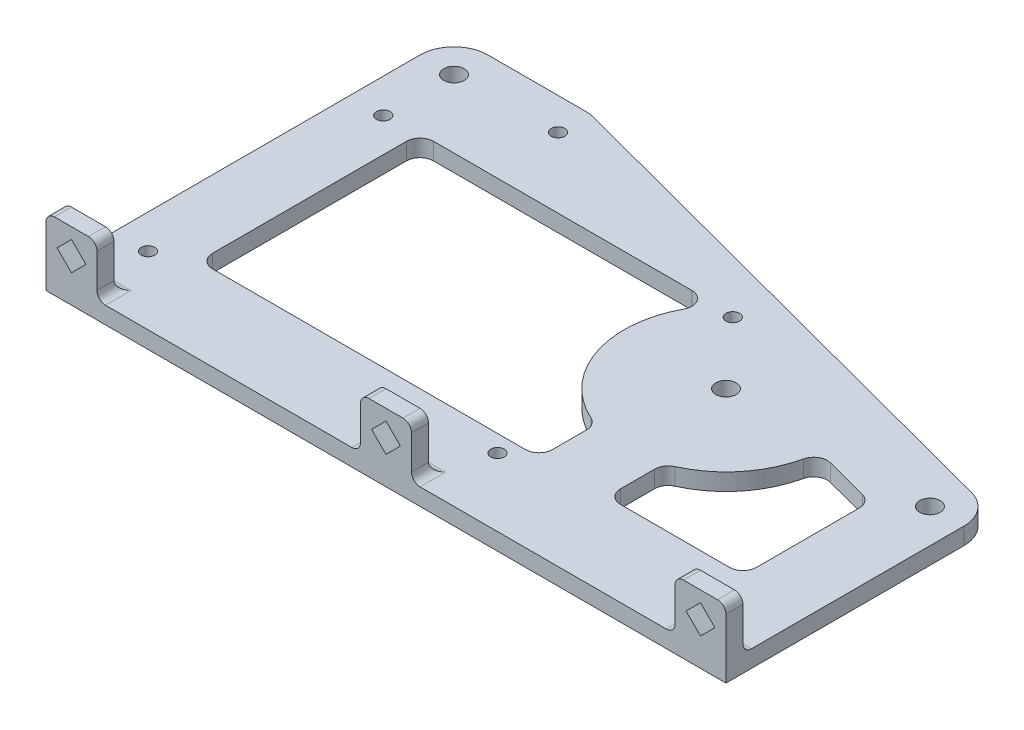
SolidWorks part; units mm, degrees
ref_plane "Front Plane" through (0, 0, 0) normal (0, 0, 1) x (1, 0, 0)
ref_plane "Top Plane" through (0, 0, 0) normal (0, 1, 0) x (1, 0, 0)
ref_plane "Right Plane" through (0, 0, 0) normal (1, 0, 0) x (0, 0, -1)
sketch "Sketch1" plane through (0, 0, 0) normal (0, 1, 0) x (1, 0, 0)
  line L0 (-57.15, 25.7742) -> (169.7943, 86.5838) construction
  line L1 (-48.962, 19.7507) -> (-53.0707, 35.0848) construction
  line L2 (-48.962, 19.7507) -> (171.8486, 78.9167) construction
  line L3 (-53.0707, 35.0848) -> (167.7399, 94.2508) construction
  line L4 (171.8486, 78.9167) -> (167.7399, 94.2508) construction
  line L5 (0, 0) -> (38.1, 0) construction
  line L6 (-82.55, 31.75) -> (-82.55, -44.45)
  line L7 (-82.55, -44.45) -> (44.45, -44.45)
  line L8 (44.45, -44.45) -> (44.45, 4.8894)
  line L9 (44.45, 4.8894) -> (-57.15, 31.75)
  line L10 (-57.15, 31.75) -> (-82.55, 31.75)
  circle A0 centre (0, 0) radius 1.905
  circle A1 centre (0, 12.7) radius 1.27 construction
  circle A2 centre (12.7, 0) radius 1.27 construction
  circle A3 centre (0, -12.7) radius 1.27 construction
  circle A4 centre (-12.7, 0) radius 1.27 construction
  circle A5 centre (0, 0) radius 12.7 construction
  circle A6 centre (-57.15, 25.7742) radius 1.27
  circle A7 centre (0, 0) radius 31.75 construction
  circle A8 centre (-76.2, 25.4) radius 1.905
  circle A9 centre (38.1, 0) radius 1.905
  dimension "D1" = 3.81
  dimension "D2" = 2.54
  dimension "D3" = 25.4
  dimension "D5" = 63.5
  dimension "D10" = 2.54
  dimension "D11" = 3.81
  dimension "D14" = 3.81
  dimension "D4" = 57.15
  dimension "D6" = 15.875
  dimension "D7" = 15
  dimension "D8" = 228.6
  dimension "D9" = 6.35
  dimension "D12" = 25.4
  dimension "D13" = 76.2
  dimension "D15" = 38.1
  dimension "D16" = 6.35
  dimension "D17" = 6.35
  dimension "D18" = 6.35
  dimension "D19" = 6.35
  dimension "D20" = 25.4
  dimension "D21" = 76.2
extrude "Boss-Extrude1" add sketch "Sketch1" along normal blind 3.175
sketch "Sketch2" plane through (0, 3.175, 0) normal (0, 1, 0) x (1, 0, 0)
  line L0 (-69.85, 10.16) -> (-69.85, -26.035)
  line L1 (-67.31, -28.575) -> (-8.89, -28.575)
  line L2 (-6.35, -26.035) -> (-6.35, -19.6748)
  line L3 (-82.55, 31.75) -> (-82.55, -44.45) construction
  line L4 (-19.05, 12.7) -> (-67.31, 12.7)
  line L5 (-57.15, 31.75) -> (-82.55, 31.75) construction
  line L6 (-82.55, -44.45) -> (44.45, -44.45) construction
  line L7 (6.35, -19.6748) -> (6.35, -26.035)
  line L8 (8.89, -28.575) -> (29.21, -28.575)
  line L9 (31.75, -26.035) -> (31.75, -6.8451)
  line L10 (29.8592, -4.3895) -> (21.7227, -2.2384)
  line L11 (44.45, -44.45) -> (44.45, 4.8894) construction
  line L12 (44.45, 4.8894) -> (-57.15, 31.75) construction
  arc A0 (-7.8441, -17.3601) -> (-16.8088, 8.9647) centre (0, 0) cw
  arc A1 (7.8441, -17.3601) -> (18.5943, -4.1418) centre (0, 0) ccw
  arc A2 (29.8592, -4.3895) -> (31.75, -6.8451) centre (29.21, -6.8451) cw
  arc A3 (29.21, -28.575) -> (31.75, -26.035) centre (29.21, -26.035) ccw
  arc A4 (8.89, -28.575) -> (6.35, -26.035) centre (8.89, -26.035) cw
  arc A5 (6.35, -19.6748) -> (7.8441, -17.3601) centre (8.89, -19.6748) cw
  arc A6 (18.5943, -4.1418) -> (21.7227, -2.2384) centre (21.0735, -4.694) cw
  arc A7 (-19.05, 12.7) -> (-16.8088, 8.9647) centre (-19.05, 10.16) cw
  arc A8 (-6.35, -19.6748) -> (-7.8441, -17.3601) centre (-8.89, -19.6748) ccw
  arc A9 (-8.89, -28.575) -> (-6.35, -26.035) centre (-8.89, -26.035) ccw
  arc A10 (-67.31, -28.575) -> (-69.85, -26.035) centre (-67.31, -26.035) cw
  arc A11 (-69.85, 10.16) -> (-67.31, 12.7) centre (-67.31, 10.16) cw
  circle A12 centre (-76.2, 12.192) radius 1.27
  circle A13 centre (-10.922, 12.192) radius 1.27
  circle A14 centre (-10.922, -31.75) radius 1.27
  circle A15 centre (-76.2, -31.75) radius 1.27
  dimension "D1" = 19.05
  dimension "D9" = 2.54
  dimension "D14" = 2.54
  dimension "D2" = 12.7
  dimension "D3" = 19.05
  dimension "D4" = 15.875
  dimension "D5" = 6.35
  dimension "D6" = 6.35
  dimension "D7" = 12.7
  dimension "D8" = 12.7
  dimension "D10" = 43.942
  dimension "D11" = 65.278
  dimension "D12" = 6.35
  dimension "D13" = 12.7
extrude "Cut-Extrude1" cut sketch "Sketch2" against normal blind 3.175
fillet "Fillet1" radius 6.35 3 edges at (44.45, 1.5875, -4.8894) (-82.55, 1.5875, -31.75) (-57.15, 1.5875, -31.75)
sketch "Sketch3" plane through (0, 0, 44.45) normal (0, 0, 1) x (1, 0, 0)
  line L0 (-82.55, 3.175) -> (-73.025, 3.175)
  line L1 (-82.55, 3.175) -> (-82.55, 12.7)
  line L2 (-73.025, 3.175) -> (-73.025, 12.7)
  line L3 (-82.55, 12.7) -> (-73.025, 12.7)
  line L4 (-82.55, 3.175) -> (44.45, 3.175) construction
  line L5 (-77.7875, 5.2434) -> (-75.0934, 7.9375)
  line L6 (44.45, 3.175) -> (34.925, 3.175)
  line L7 (44.45, 3.175) -> (44.45, 12.7)
  line L8 (44.45, 12.7) -> (34.925, 12.7)
  line L9 (34.925, 3.175) -> (34.925, 12.7)
  line L10 (-23.8125, 3.175) -> (-14.2875, 3.175)
  line L11 (-23.8125, 3.175) -> (-23.8125, 12.7)
  line L12 (-23.8125, 12.7) -> (-14.2875, 12.7)
  line L13 (-14.2875, 3.175) -> (-14.2875, 12.7)
  line L14 (-77.7875, 5.2434) -> (-80.4816, 7.9375)
  line L15 (-75.0934, 7.9375) -> (-77.7875, 10.6316)
  line L16 (-80.4816, 7.9375) -> (-77.7875, 10.6316)
  line L17 (-77.7875, 5.2434) -> (-77.7875, 10.6316) construction
  line L18 (-75.0934, 7.9375) -> (-80.4816, 7.9375) construction
  line L19 (-19.05, 5.2434) -> (-16.3559, 7.9375)
  line L20 (-19.05, 5.2434) -> (-21.7441, 7.9375)
  line L21 (-16.3559, 7.9375) -> (-19.05, 10.6316)
  line L22 (-21.7441, 7.9375) -> (-19.05, 10.6316)
  line L23 (-19.05, 5.2434) -> (-19.05, 10.6316) construction
  line L24 (-16.3559, 7.9375) -> (-21.7441, 7.9375) construction
  line L25 (39.6875, 5.2434) -> (42.3816, 7.9375)
  line L26 (39.6875, 5.2434) -> (36.9934, 7.9375)
  line L27 (42.3816, 7.9375) -> (39.6875, 10.6316)
  line L28 (36.9934, 7.9375) -> (39.6875, 10.6316)
  line L29 (39.6875, 5.2434) -> (39.6875, 10.6316) construction
  line L30 (42.3816, 7.9375) -> (36.9934, 7.9375) construction
  point P17 (-77.7875, 7.9375)
  point P18 (-19.05, 7.9375)
  point P19 (-77.7875, 7.9375)
  point P20 (-19.05, 7.9375)
  point P29 (39.6875, 7.9375)
  point P30 (39.6875, 7.9375)
  dimension "D1" = 9.525
  dimension "D2" = 9.525
  dimension "D3" = 4.7625
  dimension "D4" = 4.7625
  dimension "D5" = 3.81
  dimension "D6" = 3.81
  dimension "D7" = 4.7625
  dimension "D8" = 4.7625
  dimension "D9" = 3.81
  dimension "D10" = 4.7625
  dimension "D11" = 4.7625
  dimension "D12" = 49.2125
extrude "Boss-Extrude2" add sketch "Sketch3" against normal blind 3.175
fillet "Fillet2" radius 1.5875 13 edges at (-23.8125, 12.7, 42.8625) (-14.2875, 12.7, 42.8625) (34.925, 12.7, 42.8625) (44.45, 12.7, 42.8625) (34.925, 3.175, 42.8625) (39.6875, 3.175, 41.275) (-14.2875, 3.175, 42.8625) (-23.8125, 3.175, 42.8625) (-19.05, 3.175, 41.275) (-82.55, 12.7, 42.8625) (-73.025, 12.7, 42.8625) (-73.025, 3.175, 42.8625) (-77.7875, 3.175, 41.275)
